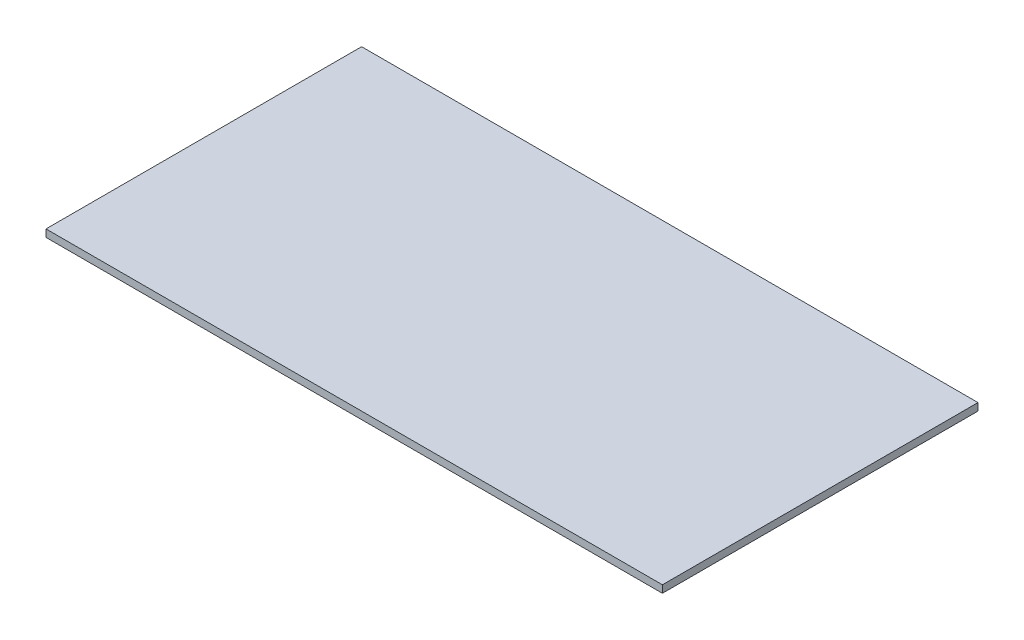
SolidWorks part; units mm, degrees
ref_plane "Front Plane" through (0, 0, 0) normal (0, 0, 1) x (1, 0, 0)
ref_plane "Top Plane" through (0, 0, 0) normal (0, 1, 0) x (1, 0, 0)
ref_plane "Right Plane" through (0, 0, 0) normal (1, 0, 0) x (0, 0, -1)
sketch "Sketch1" plane through (0, 0, 0) normal (0, 1, 0) x (1, 0, 0)
  line L1 (0, 0) -> (250, 0)
  line L2 (0, 0) -> (0, 128)
  line L3 (0, 128) -> (250, 128)
  line L4 (250, 0) -> (250, 128)
  line L5 (0, 0) -> (250, 128) construction
  line L6 (0, 128) -> (250, 0) construction
  point P4 (125, 64)
  dimension "D1" = 250
  dimension "D2" = 128
extrude "Boss-Extrude1" add sketch "Sketch1" along normal blind 3 contours L3 L4 L1 L2
